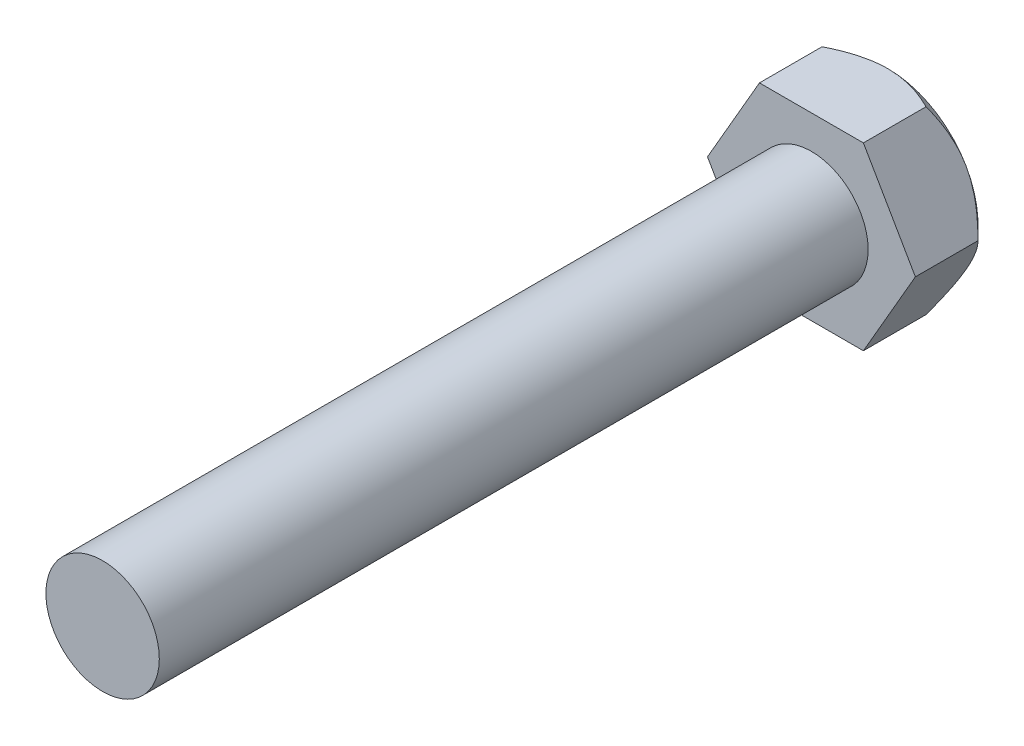
SolidWorks part; units mm, degrees
ref_plane "Plano frontal" through (0, 0, 0) normal (0, 0, 1) x (1, 0, 0)
ref_plane "Plano superior" through (0, 0, 0) normal (0, 1, 0) x (1, 0, 0)
ref_plane "Plano direito" through (0, 0, 0) normal (1, 0, 0) x (0, 0, -1)
sketch "Esboço1" plane through (0, 0, 0) normal (0, 0, 1) x (1, 0, 0)
  line L1 (3.6662, -6.35) -> (7.3323, 0)
  line L2 (7.3323, 0) -> (3.6662, 6.35)
  line L3 (3.6662, 6.35) -> (-3.6662, 6.35)
  line L4 (-3.6662, 6.35) -> (-7.3323, 0)
  line L5 (-7.3323, 0) -> (-3.6662, -6.35)
  line L6 (-3.6662, -6.35) -> (3.6662, -6.35)
  circle A0 centre (0, 0) radius 6.35 construction
extrude "Ressalto-extrusão1" add sketch "Esboço1" along normal blind 5.4
sketch "Esboço2" plane through (0, 0, 5.4) normal (0, 0, 1) x (1, 0, 0)
  circle A0 centre (0, 0) radius 4
extrude "Ressalto-extrusão2" add sketch "Esboço2" along normal blind 50
sketch "Esboço3" plane through (0, 0, 0) normal (0, 0, -1) x (-1, 0, 0)
  line L0 (7.3323, 0) -> (3.6662, -6.35) construction
  circle A0 centre (0, 0) radius 6.35
extrude "Corte-extrusão1" cut sketch "Esboço3" against normal blind 65 draft 45 flip side to cut
